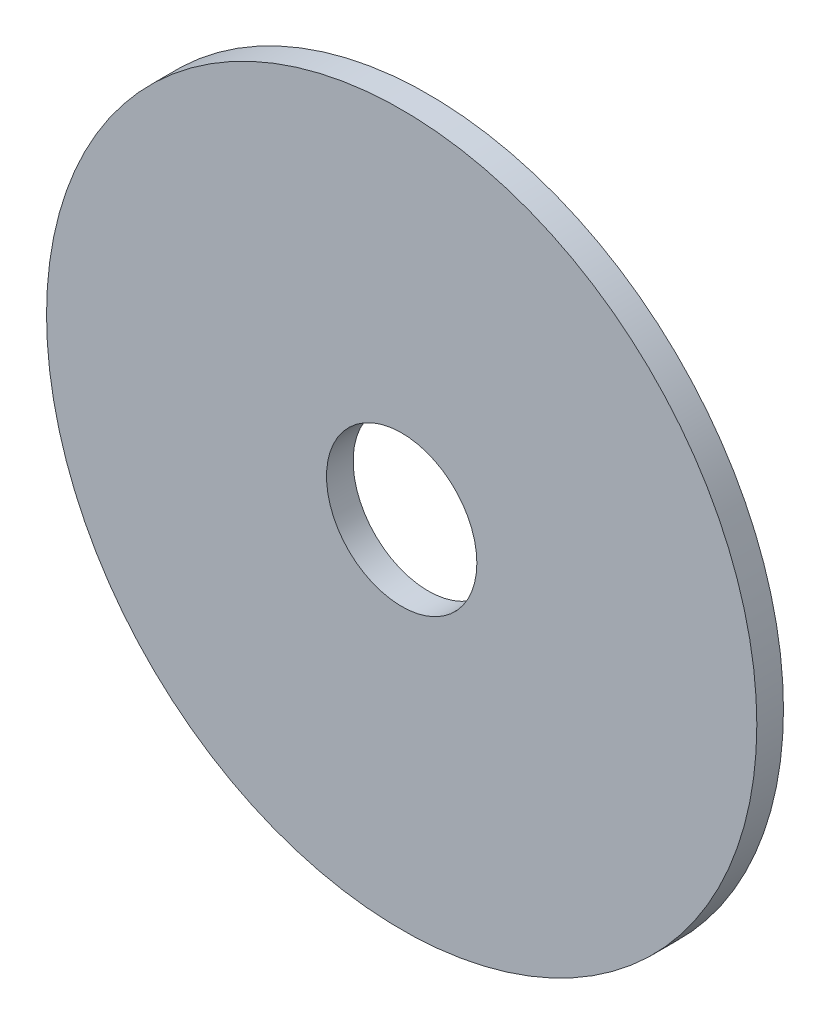
SolidWorks part; units mm, degrees
ref_plane "Front Plane" through (0, 0, 0) normal (0, 0, 1) x (1, 0, 0)
ref_plane "Top Plane" through (0, 0, 0) normal (0, 1, 0) x (1, 0, 0)
ref_plane "Right Plane" through (0, 0, 0) normal (1, 0, 0) x (0, 0, -1)
sketch "Sketch1" plane through (0, 0, 0) normal (0, 0, 1) x (1, 0, 0)
  circle A0 centre (0, 0) radius 60
  circle A1 centre (0, 0) radius 12.7
  dimension "D1" = 120
  dimension "D2" = 25.4
extrude "Boss-Extrude1" add sketch "Sketch1" along normal blind 4.5
equation "\"D1@Boss-Extrude1\"=\"mat@v5.assembly\""
